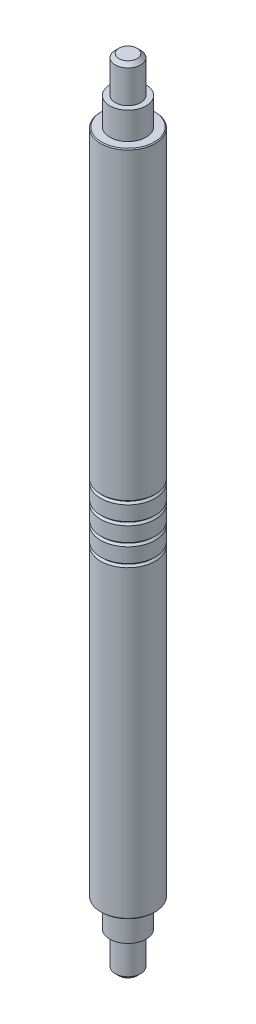
SolidWorks part; units mm, degrees
ref_plane "Front Plane" through (0, 0, 0) normal (0, 0, 1) x (1, 0, 0)
ref_plane "Top Plane" through (0, 0, 0) normal (0, 1, 0) x (1, 0, 0)
ref_plane "Right Plane" through (0, 0, 0) normal (1, 0, 0) x (0, 0, -1)
sketch "Sketch1" plane through (0, 0, 0) normal (0, 1, 0) x (1, 0, 0)
  circle A0 centre (0, 0) radius 1.5
  dimension "D1" = 3
extrude "Boss-Extrude1" add sketch "Sketch1" along normal blind 43.75
sketch "Sketch2" plane through (0, 43.75, 0) normal (0, 1, 0) x (1, 0, 0)
  circle A0 centre (0, 0) radius 1
  dimension "D1" = 2
extrude "Cut-Extrude1" cut sketch "Sketch2" against normal blind 3.5 flip side to cut
sketch "Sketch3" plane through (0, 43.75, 0) normal (0, 1, 0) x (1, 0, 0)
  circle A0 centre (0, 0) radius 0.7
  dimension "D1" = 1.4
extrude "Cut-Extrude2" cut sketch "Sketch3" against normal blind 2 flip side to cut
cosmetic thread "Cosmetic Thread1" parameters "D2"=1.057
sketch "Sketch4" plane through (0, 0, 0) normal (0, -1, 0) x (1, 0, 0)
  circle A0 centre (0, 0) radius 1 construction
  circle A1 centre (0, 0) radius 1
extrude "Cut-Extrude5" cut sketch "Sketch4" against normal offset from surface (3.5 mm away) 36.75 flip side to cut up to face at (0, 40.25, 1)
sketch "Sketch5" plane through (0, 0, 0) normal (0, -1, 0) x (1, 0, 0)
  circle A0 centre (0, 0) radius 0.7 construction
  circle A1 centre (0, 0) radius 0.7
extrude "Cut-Extrude6" cut sketch "Sketch5" against normal offset from surface (2 mm away) 1.5 flip side to cut up to face at (0, 3.5, 1)
cosmetic thread "Cosmetic Thread2" parameters "D2"=1.057
sketch "Sketch6" plane through (0, 0, 0) normal (0, 0, 1) x (1, 0, 0)
  line L0 (0, 43.75) -> (0, 2.7768) construction
  line L1 (0.7, 43.75) -> (-0.7, 43.75) construction
  line L2 (-1.5, 23.475) -> (-1.4, 23.375)
  line L3 (-1.5, 40.25) -> (-1.5, 3.5) construction
  line L4 (-1.4, 23.375) -> (-1.5, 23.275)
  line L5 (-1.4, 23.375) -> (-2.2691, 23.375) construction
  line L6 (1.5, 40.25) -> (-1.5, 40.25) construction
  line L7 (-1.5, 23.475) -> (-1.5, 23.275)
  dimension "D1" = 0.1
  dimension "D2" = 16.875
revolve "Cut-Revolve1" cut sketch "Sketch6" angle 360 about L0
pattern_linear "LPattern1" count 4 spacing 1 along (0, -1, 0) of "Cut-Revolve1"
chamfer "Chamfer3" distance 0.2 angle 45 2 edges at (0, 43.75, 0.7) (0, 0, -0.7)
chamfer "Chamfer4" distance 0.05 angle 45 2 edges at (0, 3.5, 1.5) (0, 40.25, 1.5)
ref_plane "Plane1" through (0, 22.875, 0) normal (0, 1, 0) x (1, 0, 0)
